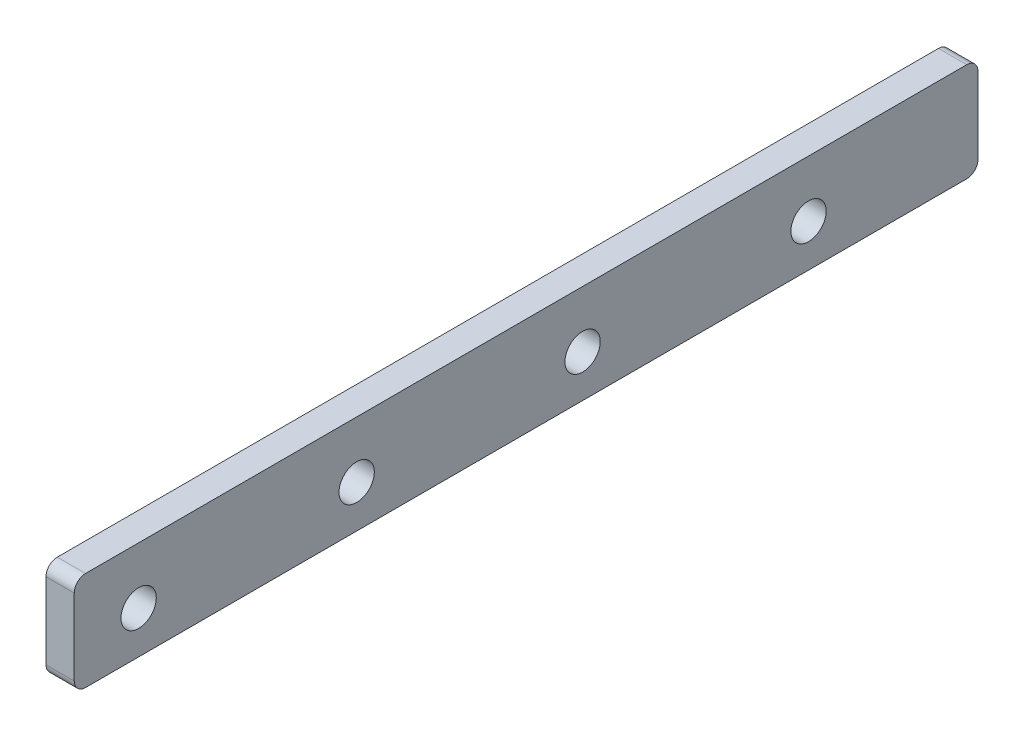
SolidWorks part; units mm, degrees
material "6061-T6 (SS)"
ref_plane "Front Plane" through (0, 0, 0) normal (0, 0, 1) x (1, 0, 0)
ref_plane "Top Plane" through (0, 0, 0) normal (0, 1, 0) x (1, 0, 0)
ref_plane "Right Plane" through (0, 0, 0) normal (1, 0, 0) x (0, 0, -1)
sketch "Sketch1" plane through (0, 0, 0) normal (1, 0, 0) x (0, 0, -1)
  line L0 (0, 12.7) -> (155.575, 12.7) construction
  line L1 (0, 0) -> (155.575, 0)
  line L2 (0, 0) -> (0, 25.4)
  line L3 (0, 25.4) -> (155.575, 25.4)
  line L4 (155.575, 0) -> (155.575, 25.4)
  line L5 (-47.625, 12.7) -> (0, 12.7) construction
  line L6 (0, 25.4) -> (-47.625, 25.4)
  line L7 (0, 25.4) -> (0, 0)
  line L8 (0, 0) -> (-47.625, 0)
  line L9 (-47.625, 25.4) -> (-47.625, 0)
  line L10 (-47.625, 3.175) -> (155.575, 3.175)
  circle A0 centre (15.875, 12.7) radius 3.9688
  circle A1 centre (66.675, 12.7) radius 3.9687
  circle A2 centre (117.475, 12.7) radius 3.9688
  circle A3 centre (-33.147, 12.7) radius 3.9688
  dimension "D3" = 7.9375
  dimension "D8" = 7.9375
  dimension "D1" = 50.8
  dimension "D2" = 50.8
  dimension "D4" = 15.875
  dimension "D5" = 38.1
  dimension "D6" = 12.7
  dimension "D7" = 49.022
  dimension "D9" = 47.625
  dimension "D10" = 3.175
extrude "Boss-Extrude1" add sketch "Sketch1" along normal blind 6.35 contours L6 L9 L8 L2 A3 | L1 L4 L3 L2 A2 A1 A0
fillet "Fillet1" radius 2.54 4 edges at (3.175, 25.4, -155.575) (3.175, 25.4, 47.625) (3.175, 3.175, 47.625) (3.175, 3.175, -155.575)
